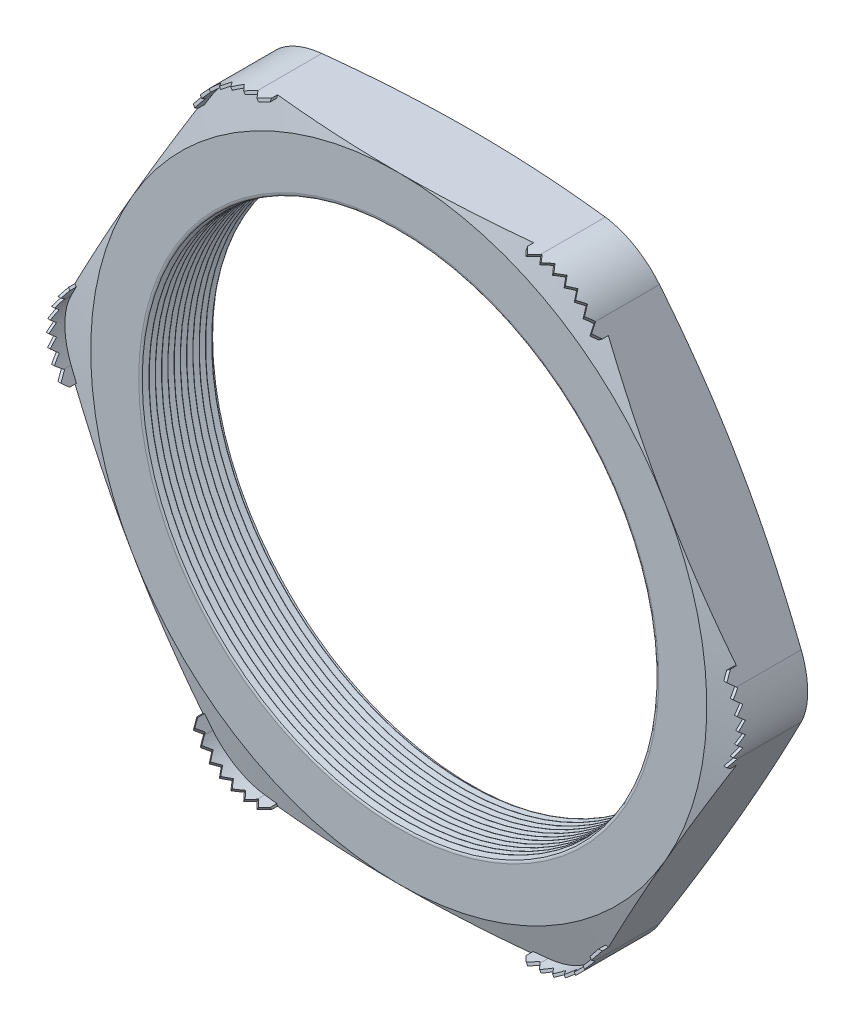
SolidWorks part; units mm, degrees
ref_plane "Front Plane" through (0, 0, 0) normal (0, 0, 1) x (1, 0, 0)
ref_plane "Top Plane" through (0, 0, 0) normal (0, 1, 0) x (1, 0, 0)
ref_plane "Right Plane" through (0, 0, 0) normal (1, 0, 0) x (0, 0, -1)
sketch "Sketch1" plane through (0, 0, 0) normal (0, 0, 1) x (1, 0, 0)
  line L1 (-17.3043, 0) -> (-8.6522, -14.986)
  line L2 (-8.6522, -14.986) -> (8.6522, -14.986)
  line L3 (8.6522, -14.986) -> (17.3043, 0)
  line L4 (17.3043, 0) -> (8.6522, 14.986)
  line L5 (8.6522, 14.986) -> (-8.6522, 14.986)
  line L6 (-8.6522, 14.986) -> (-17.3043, 0)
  circle A0 centre (0, 0) radius 14.986 construction
  circle A1 centre (0, 0) radius 12.446
  dimension "TS" = 24.892
  dimension "H" = 29.972
extrude "Extrude1" add sketch "Sketch1" along normal blind 3.556
fillet "Fillet1" radius 3.048 6 edges at (-8.6522, 14.986, 1.778) (-17.3043, 0, 1.778) (-8.6522, -14.986, 1.778) (8.6522, -14.986, 1.778) (17.3043, 0, 1.778) (8.6522, 14.986, 1.778)
sketch "Sketch2" plane through (0, 0, 3.556) normal (0, 0, 1) x (1, 0, 0)
  line L0 (-6.8924, 14.986) -> (-6.232, 14.986)
  line L1 (6.8924, 14.986) -> (-6.8924, 14.986) construction
  line L2 (-9.5321, 13.462) -> (-9.8623, 12.8901)
  line L3 (-9.5321, 13.462) -> (-16.4245, 1.524) construction
  line L4 (-6.8924, 14.859) -> (-6.232, 14.859)
  line L5 (-9.4221, 13.3985) -> (-9.7523, 12.8266)
  line L6 (-9.8623, 12.8901) -> (-9.7523, 12.8266)
  line L7 (-6.232, 14.986) -> (-6.232, 14.859)
  arc A0 (-6.8924, 14.859) -> (-9.4221, 13.3985) centre (-6.8924, 11.938) ccw
  arc A1 (-6.8924, 14.986) -> (-9.5321, 13.462) centre (-6.8924, 11.938) ccw construction
  arc A4 (-6.8924, 14.986) -> (-9.5321, 13.462) centre (-6.8924, 11.938) ccw
  dimension "D1" = 0.6604
  dimension "D2" = 0.6604
  dimension "OFFSET" = 0.127
fillet "Fillet3" radius 0.2032 2 edges at (12.446, 0, 0) (12.446, 0, 3.556)
sketch "Sketch3" plane through (0, 0, 0) normal (0, 1, 0) x (1, 0, 0)
  line L0 (-12.446, -3.556) -> (-12.446, -3.2627)
  line L2 (-12.446, -3.2627) -> (-12.7, -3.4094)
  line L3 (-12.7, -3.4094) -> (-12.446, -3.556)
  line L4 (-12.446, -0.2032) -> (-12.446, -3.3528) construction
  line L5 (-9.5321, -3.556) -> (-16.4245, -3.556) construction
  dimension "D1" = 60
  dimension "D2" = 60
  dimension "D3" = 0.254
revolve "Cut-Revolve1" cut sketch "Sketch3" angle 360 about axis through (0, 0, 3.556) along (0, 0, -1)
pattern_linear "LPattern1" count 12 spacing 0.3048 along (0, 0, -1) of "Cut-Revolve1"
sketch "Sketch4" plane through (0, 0, 0) normal (0, 0, -1) x (-1, 0, 0)
  line L0 (-16.4245, 1.524) -> (-9.5321, 13.462) construction
  circle A0 centre (0, 0) radius 14.986
extrude "Cut-Extrude1" cut sketch "Sketch4" against normal through all draft 75 flip side to cut
sketch "Sketch5" plane through (0, 0, 3.556) normal (0, 0, 1) x (1, 0, 0)
  line L0 (6.8924, 14.986) -> (-6.8924, 14.986) construction
  circle A0 centre (0, 0) radius 14.986
extrude "Cut-Extrude2" cut sketch "Sketch5" against normal through all draft 75 flip side to cut
extrude "Extrude2" add sketch "Sketch2" along normal blind 0.8382 and the other way up to next
ref_plane "Plane1" through (-7.9921, 13.8428, 0) normal (0.5, -0.866, 0) x (0.866, 0.5, 0)
sketch "Sketch7" plane through (-7.9921, 13.8428, 0) normal (0.5, -0.866, 0) x (0.866, 0.5, 0)
  line L0 (-2.0959, 3.5141) -> (-1.7911, 3.8661)
  line L1 (-2.0959, 3.2226) -> (-2.0959, 4.3942) construction
  line L2 (0, 1.3136) -> (0, 4.0135) construction
  line L4 (-1.7911, 3.8661) -> (-1.4863, 3.5141)
  line L5 (-0.6096, 3.8661) -> (-0.3048, 3.5141)
  line L6 (-1.2192, 3.8661) -> (-0.9144, 3.5141)
  line L7 (-0.3048, 3.5141) -> (0, 3.8661)
  line L8 (0, 3.8661) -> (0.3048, 3.5141)
  line L10 (0.6096, 3.8661) -> (0.9144, 3.5141)
  line L11 (1.2192, 3.8661) -> (1.524, 3.5141)
  line L12 (-1.4863, 3.5141) -> (-1.2192, 3.8661)
  line L13 (-0.9144, 3.5141) -> (-0.6096, 3.8661)
  line L14 (0.3048, 3.5141) -> (0.6096, 3.8661)
  line L15 (1.7911, 3.8661) -> (2.0959, 3.5141)
  line L16 (2.0959, 3.2226) -> (2.0959, 4.3942) construction
  line L17 (-2.0959, 3.5141) -> (-2.0959, 4.3942)
  line L19 (-2.0959, 4.3942) -> (2.0959, 4.3942)
  line L20 (2.0959, 4.3942) -> (2.0959, 3.5141)
  line L23 (0.9144, 3.5141) -> (1.2192, 3.8661)
  line L25 (1.524, 3.5141) -> (1.7911, 3.8661)
  dimension "D1" = 0.8801
  dimension "D2" = 0.5281
  dimension "D3" = 0.3048
extrude "Cut-Extrude4" cut sketch "Sketch7" against normal through all
pattern_circular "CirPattern1" count 6 over 360 about axis through (0, 0, 0) along (0, 0, 1) of "Extrude2"
pattern_circular "CirPattern2" count 6 over 360 about axis through (0, 0, 0) along (0, 0, 1) of "Cut-Extrude4"
